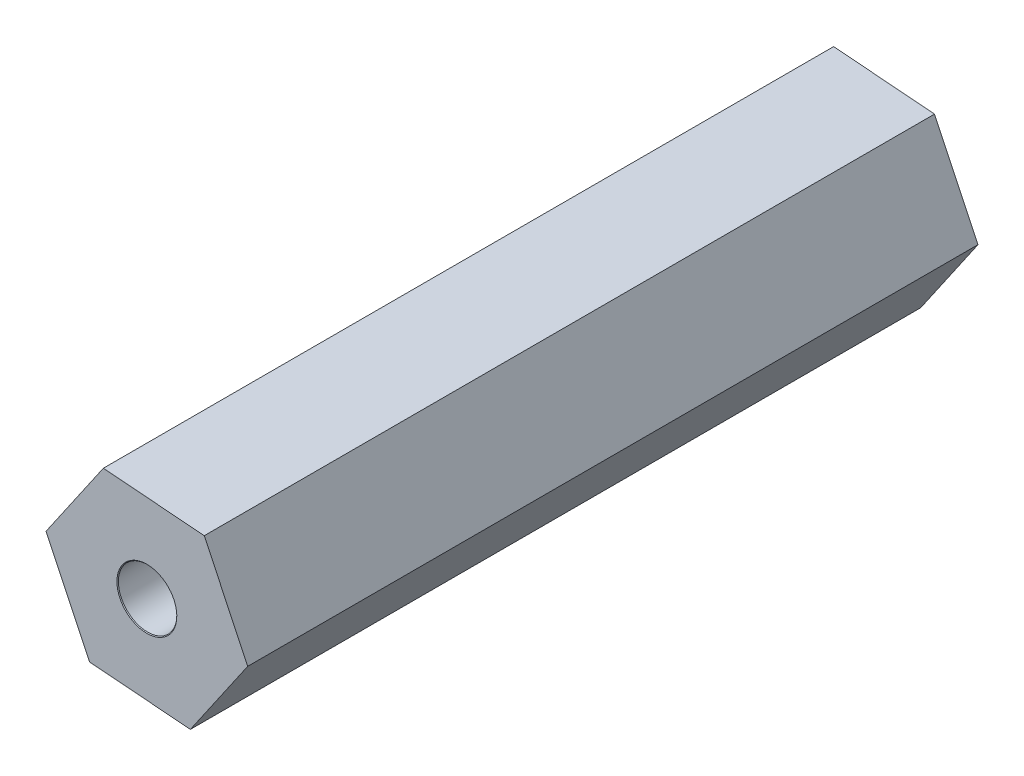
SolidWorks part; units mm, degrees
ref_plane "Front Plane" through (0, 0, 0) normal (0, 0, 1) x (1, 0, 0)
ref_plane "Top Plane" through (0, 0, 0) normal (0, 1, 0) x (1, 0, 0)
ref_plane "Right Plane" through (0, 0, 0) normal (1, 0, 0) x (0, 0, -1)
sketch "Sketch1" plane through (0, 0, 0) normal (0, 0, 1) x (1, 0, 0)
  line L1 (-60.4888, 110.1278) -> (-62.4532, 107.2746)
  line L2 (-62.4532, 107.2746) -> (-60.9644, 104.1467)
  line L3 (-60.9644, 104.1467) -> (-57.5112, 103.8722)
  line L4 (-57.5112, 103.8722) -> (-55.5468, 106.7254)
  line L5 (-55.5468, 106.7254) -> (-57.0356, 109.8533)
  line L6 (-57.0356, 109.8533) -> (-60.4888, 110.1278)
  circle A0 centre (-59, 107) radius 3 construction
  point P1 (-61.7088, 105.7106)
  dimension "D1" = 6
extrude "Boss-Extrude1" add sketch "Sketch1" along normal up to surface (25 mm away)
hole_wizard "Ø2.0mm Dowel Hole1" positions "3DSketch1" profile "Sketch2" hole size "Ø2.0" standard "ISO"
sketch3d "3DSketch1"
  line L0 (-62.4532, 107.2746, 25) -> (-55.5468, 106.7254, 25) construction
  point P4 (-59, 107, 25)
sketch "Sketch2" plane through (-59, 107, 25) normal (1, 0, 0) x (0, -1, 0)
  line L0 (0, 0) -> (0, 25.6009)
  line L1 (0, 25.6009) -> (1, 25)
  line L2 (1, 25) -> (1, 0.025)
  line L3 (1, 0.025) -> (1.025, 0)
  line L5 (1.025, 0) -> (0, 0)
  line L6 (-1, 0.025) -> (-1.025, 0) construction
  line L10 (0, 25.6009) -> (-1, 25) construction
  line L11 (0, -6.35) -> (0, 107.95) construction
  dimension "Hole Dia." = 2
  dimension "Hole Depth" = 25
  dimension "Near C'Sink Dia." = 2.05
  dimension "Near C'Sink Angle" = 90
  dimension "Drill Angle" = 118
